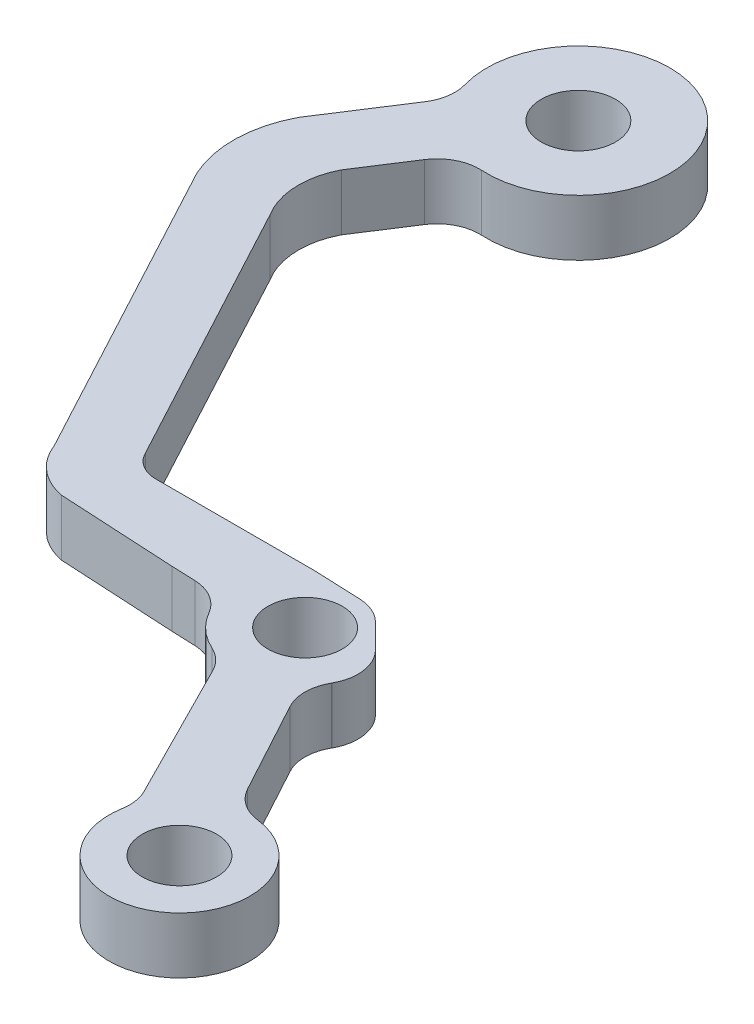
SolidWorks part; units mm, degrees
material "PLA"
ref_plane "Front Plane" through (0, 0, 0) normal (0, 0, 1) x (1, 0, 0)
ref_plane "Top Plane" through (0, 0, 0) normal (0, 1, 0) x (1, 0, 0)
ref_plane "Right Plane" through (0, 0, 0) normal (1, 0, 0) x (0, 0, -1)
ref_plane "Plane1" through (0, 4, 0) normal (0, 1, 0) x (1, 0, 0)
sketch "Sketch1" plane through (0, 4, 0) normal (0, 1, 0) x (1, 0, 0)
  line L0 (80.4223, 54.0505) -> (76.8536, 60.6323)
  line L1 (76.4012, 67.1578) -> (74.7101, 68.8489)
  line L2 (72.7129, 69.725) -> (69.3416, 69.8647)
  line L3 (69.3416, 69.8647) -> (58.0479, 69.8647)
  line L4 (56.116, 71.1054) -> (45.9135, 90.14)
  line L5 (45.662, 95.4669) -> (47.9844, 99.0605)
  line L6 (44.4478, 102.6467) -> (40.9177, 97.1844)
  line L7 (40.7298, 90.14) -> (52.4488, 68.2763)
  line L8 (55.7376, 65.5195) -> (64.0439, 65.0687)
  line L9 (64.0439, 65.0687) -> (65.737, 65.0024)
  line L10 (71.9047, 60.0912) -> (76.8866, 50.2358)
  arc A0 (76.8536, 60.6323) -> (76.8838, 63.5466) centre (79.4909, 62.0623) cw
  arc A1 (76.8838, 63.5466) -> (76.8918, 63.5606) centre (72.5387, 66.0204) ccw
  arc A2 (76.8918, 63.5606) -> (76.4012, 67.1578) centre (74.2799, 65.0365) ccw
  arc A3 (74.7101, 68.8489) -> (72.7129, 69.725) centre (72.5888, 66.7276) ccw
  arc A4 (58.0479, 69.8647) -> (56.116, 71.1054) centre (58.0835, 72.0445) cw
  arc A5 (45.9135, 90.14) -> (45.662, 95.4669) centre (50.4346, 93.0228) cw
  arc A6 (47.9844, 99.0605) -> (50.6776, 100.4271) centre (50.504, 97.4322) cw
  arc A7 (50.6776, 100.4271) -> (44.8098, 105.1091) centre (51.0536, 106.9163) ccw
  arc A8 (44.8098, 105.1091) -> (44.4478, 102.6467) centre (41.9281, 104.275) cw
  arc A9 (40.9177, 97.1844) -> (40.7298, 90.14) centre (47.9508, 93.4721) ccw
  arc A10 (52.4488, 68.2763) -> (55.7376, 65.5195) centre (56.5568, 69.837) ccw
  arc A11 (65.737, 65.0024) -> (68.2142, 63.5105) centre (65.6195, 62.0047) cw
  arc A12 (68.2142, 63.5105) -> (70.4691, 61.4688) centre (72.5387, 66.0204) ccw
  arc A13 (70.4691, 61.4688) -> (71.9047, 60.0912) centre (69.2274, 58.7378) cw
  arc A14 (76.8866, 50.2358) -> (77.1666, 48.3786) centre (74.2092, 48.8824) cw
  arc A15 (77.1666, 48.3786) -> (82.6981, 52.5023) centre (82.0956, 47.5388) ccw
  arc A16 (82.6981, 52.5023) -> (80.4223, 54.0505) centre (83.0596, 55.4805) cw
  circle A17 centre (51.0536, 106.9163) radius 2.6375
  circle A18 centre (82.0956, 47.5388) radius 2.6375
  circle A19 centre (72.5387, 66.0204) radius 2.6375
extrude "Boss-Extrude1" add sketch "Sketch1" against normal blind 4
